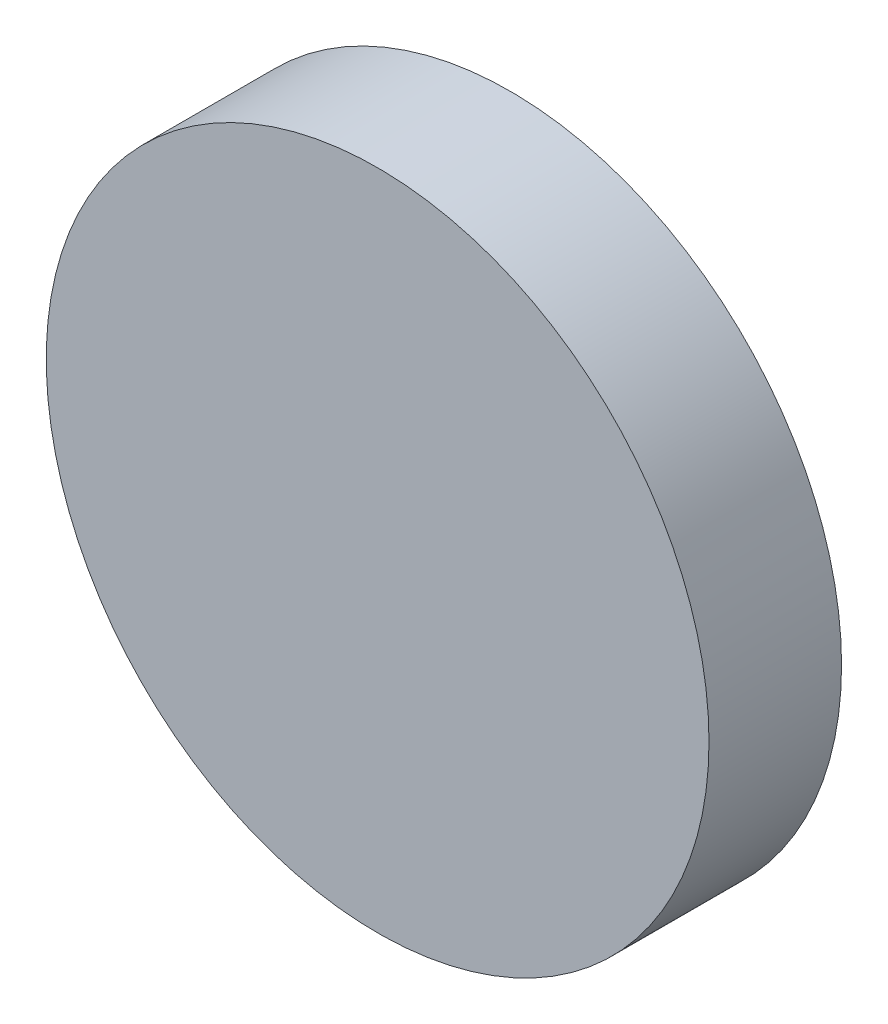
SolidWorks part; units mm, degrees
ref_plane "Front Plane" through (0, 0, 0) normal (0, 0, 1) x (1, 0, 0)
ref_plane "Top Plane" through (0, 0, 0) normal (0, 1, 0) x (1, 0, 0)
ref_plane "Right Plane" through (0, 0, 0) normal (1, 0, 0) x (0, 0, -1)
sketch "Sketch1" plane through (0, 0, 0) normal (0, 0, 1) x (1, 0, 0)
  circle A0 centre (0, 0) radius 2.5
  dimension "D1" = 5
extrude "Boss-Extrude1" add sketch "Sketch1" along normal blind 1
